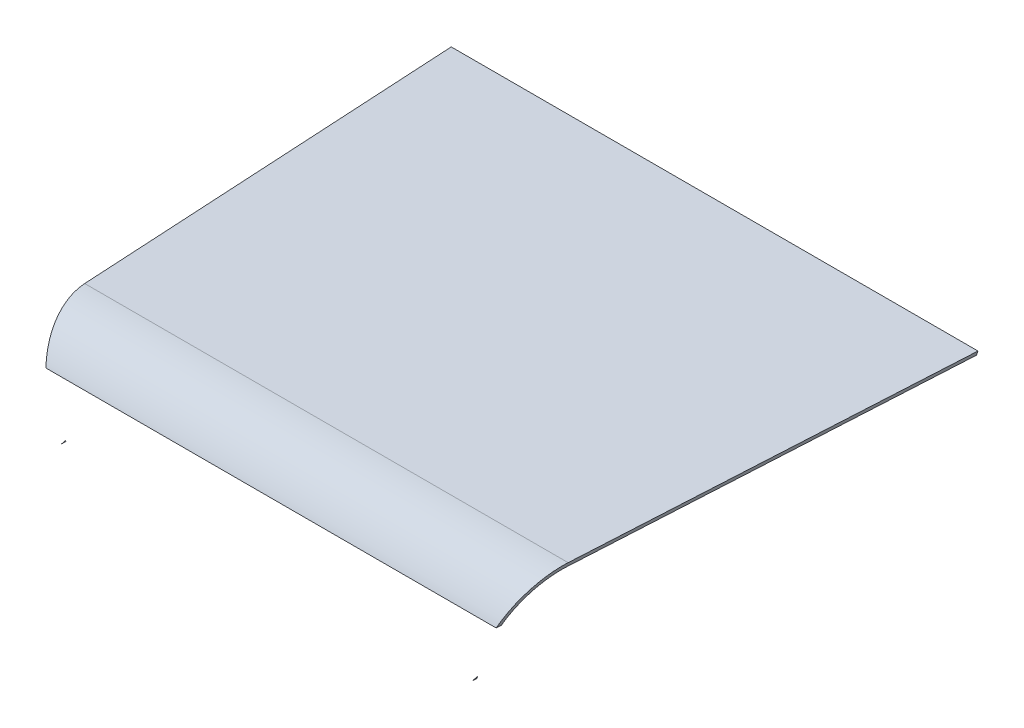
SolidWorks part; units mm, degrees
material "AISI 316 Stainless Steel Sheet (SS)"
ref_plane "Front Plane" through (0, 0, 0) normal (0, 0, 1) x (1, 0, 0)
ref_plane "Top Plane" through (0, 0, 0) normal (0, 1, 0) x (1, 0, 0)
ref_plane "Right Plane" through (0, 0, 0) normal (1, 0, 0) x (0, 0, -1)
sketch "Sketch1" plane through (0, 0, 0) normal (0, 0, 1) x (1, 0, 0)
  line L4 (-159.6663, 250) -> (-137.5, 189.0986)
  line L5 (-137.5, 189.0986) -> (137.5, 189.0986)
  line L6 (137.5, 189.0986) -> (159.6663, 250)
  line L7 (159.6663, 250) -> (-159.6663, 250)
  line L8 (-159.6663, 250) -> (-137.5, 189.0986)
  line L9 (-137.5, 189.0986) -> (137.5, 189.0986)
  line L10 (137.5, 189.0986) -> (159.6663, 250)
  line L11 (159.6663, 250) -> (-159.6663, 250)
  dimension "D1" = 0
ref_plane "Plane1" through (0, 0, -300) normal (0, 0, 1) x (1, 0, 0)
sketch "Sketch2" plane through (0, 0, -300) normal (0, 0, 1) x (1, 0, 0)
  line L4 (-154.2314, 189.0986) -> (154.2314, 189.0986)
  line L5 (154.2314, 189.0986) -> (176.3977, 250)
  line L6 (176.3977, 250) -> (-176.3977, 250)
  line L7 (-176.3977, 250) -> (-154.2314, 189.0986)
  dimension "D1" = 70
  dimension "D2" = 70
  dimension "D3" = 308.4627
  dimension "D4" = 110
loft "Loft1" add profiles "Sketch2", "Sketch1"
fillet "Fillet1" radius 40 1 edges
shell "Shell2" thickness 3
ref_plane "Plane2" through (0, 0, 0) normal (0, 0, 1) x (1, 0, 0)
sketch "Sketch4" plane through (0, 0, 0) normal (0, 0, 1) x (1, 0, 0)
  line L0 (-137.5, 189.0986) -> (137.5, 189.0986)
  line L1 (137.5, 189.0986) -> (154.249, 225.0586)
  line L2 (154.249, 225.0586) -> (-165.3718, 225.0586)
  line L3 (-165.3718, 225.0586) -> (-137.5, 189.0986)
  dimension "D1" = 52.222
  dimension "D2" = 65.025
  dimension "D3" = 35.96
extrude "Cut-Extrude1" cut sketch "Sketch4" against normal blind 30
